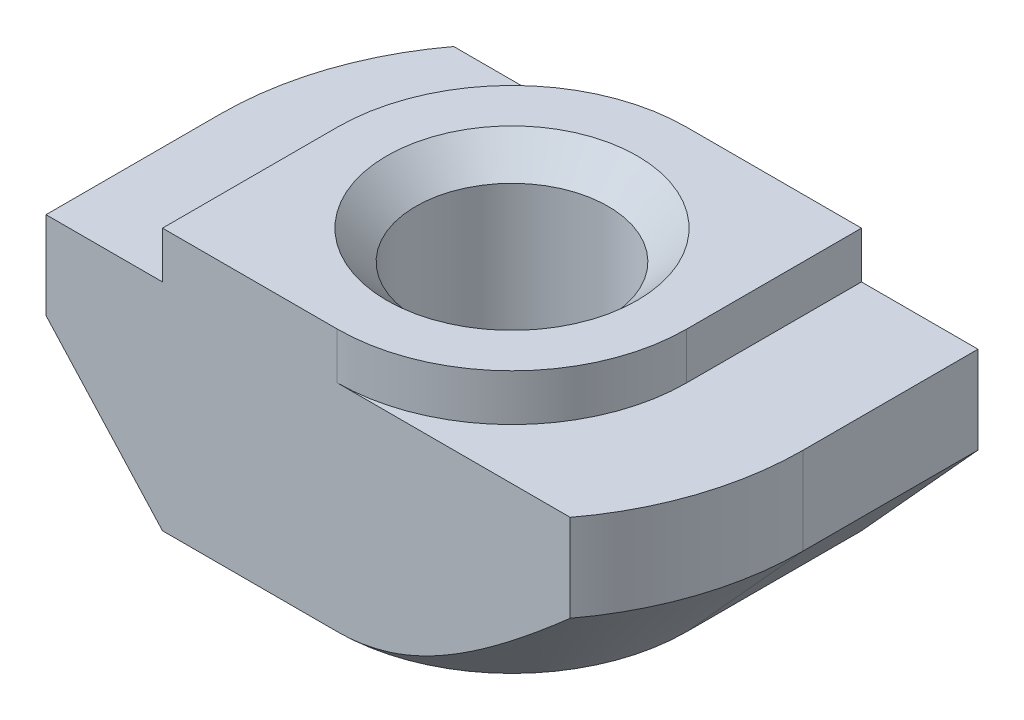
SolidWorks part; units mm, degrees
material "Сталь 20  ГОСТ 1050-2013"
ref_plane "Спереди" through (0, 0, 0) normal (0, 0, 1) x (1, 0, 0)
ref_plane "Сверху" through (0, 0, 0) normal (0, 1, 0) x (1, 0, 0)
ref_plane "Справа" through (0, 0, 0) normal (1, 0, 0) x (0, 0, -1)
sketch "Эскиз1" plane through (0, 0, 0) normal (0, 0, 1) x (1, 0, 0)
  line L0 (3, 0) -> (-3, 0)
  line L1 (-3, 0) -> (-3, -0.8)
  line L2 (-3, -0.8) -> (-5, -0.8)
  line L3 (-5, -0.8) -> (-5, -4.5)
  line L4 (-5, -4.5) -> (5, -4.5)
  line L5 (0, -4.5) -> (0, 0) construction
  line L6 (5, -0.8) -> (5, -4.5)
  line L7 (3, -0.8) -> (5, -0.8)
  line L8 (3, 0) -> (3, -0.8)
  dimension "D1" = 6
  dimension "D2" = 10
  dimension "D3" = 4.5
  dimension "D4" = 0.8
extrude "Бобышка-Вытянуть1" add sketch "Эскиз1" along normal mid plane 6
hole_wizard "Отверстие обработанное метчиком M41" positions "Эскиз2" profile "Эскиз3" tap size "M4" standard "ISO" end condition up to next
sketch "Эскиз2" plane through (0, 0, 0) normal (0, 1, 0) x (1, 0, 0)
  point P0 (0, 0)
sketch "Эскиз3" plane through (0, 0, 0) normal (1, 0, 0) x (0, 0, 1)
  line L0 (0, 0) -> (0, 4.5)
  line L1 (0, 4.5) -> (2.15, 4.5)
  line L2 (1.65, 4) -> (1.65, 0.5)
  line L3 (1.65, 0.5) -> (2.15, 0)
  line L5 (2.15, 0) -> (0, 0)
  line L6 (-1.65, 0.5) -> (-2.15, 0) construction
  line L7 (2.15, 4.5) -> (1.65, 4)
  line L8 (-2.15, 4.5) -> (-1.65, 4) construction
  line L11 (0, -6.35) -> (0, 107.95) construction
  dimension "Диаметр проходного сверла" = 3.3
  dimension "Глубина проходного сверла" = 4.5
  dimension "Диаметр передней зенковки" = 4.3
  dimension "Угол передней зенковки" = 90
  dimension "Диаметр задней зенковки" = 4.3
  dimension "Угол задней зенковки" = 90
cosmetic thread "Отверстие резьбы1" parameters "D2"=4
sketch "Эскиз4" plane through (0, 0, 0) normal (0, 1, 0) x (1, 0, 0)
  line L0 (-3, 3) -> (-3, 0)
  line L1 (-3, -3) -> (-3, 3) construction
  line L2 (3, 3) -> (-3, 3) construction
  line L3 (0, 3) -> (-3, 3)
  line L4 (0, -3) -> (3, -3)
  line L5 (3, -3) -> (-3, -3) construction
  line L6 (3, -3) -> (3, 0)
  line L7 (3, -3) -> (3, 3) construction
  arc A0 (-3, 0) -> (0, 3) centre (0, 0) cw
  arc A1 (3, 0) -> (0, -3) centre (0, 0) cw
extrude "Вырез-Вытянуть1" cut sketch "Эскиз4" against normal up to surface (0.8 mm away) up to face at (-4, -0.8, 0)
sketch "Эскиз5" plane through (0, -0.8, 0) normal (0, 1, 0) x (1, 0, 0)
  line L0 (-5, 0) -> (-5, 3)
  line L1 (-5, -3) -> (-5, 3) construction
  line L2 (-5, 3) -> (-4, 3)
  line L3 (0, 3) -> (-5, 3) construction
  line L4 (5, 0) -> (5, -3)
  line L5 (5, -3) -> (5, 3) construction
  line L6 (5, -3) -> (4, -3)
  line L7 (5, -3) -> (0, -3) construction
  arc A0 (-4, 3) -> (-5, 0) centre (0, 0) ccw
  arc A2 (5, 0) -> (4, -3) centre (0, 0) cw
  point P19 (0, 0)
extrude "Вырез-Вытянуть2" cut sketch "Эскиз5" against normal through all
sketch "Эскиз6" plane through (0, 0, 3) normal (0, 0, 1) x (1, 0, 0)
  line L0 (-5, -2.3) -> (-5, -4.5)
  line L1 (-5, -0.8) -> (-5, -4.5) construction
  line L2 (-5, -4.5) -> (-3, -4.5)
  line L3 (-5, -4.5) -> (4, -4.5) construction
  line L4 (-3, -4.5) -> (-5, -2.3)
  line L5 (-3, -0.8) -> (-5, -0.8) construction
  line L6 (-3, 0) -> (-3, -0.8) construction
  point P10 (0, 0)
  dimension "D1" = 1.5
sketch "Эскиз7" plane through (0, -4.5, 0) normal (0, -1, 0) x (1, 0, 0)
  line L0 (0, 5) -> (-5, 5)
  line L1 (-5, 5) -> (-5, 0)
  line L2 (0, -5) -> (5, -5)
  line L3 (5, -5) -> (5, 0)
  arc A0 (-5, 0) -> (0, -5) centre (0, 0) ccw
  arc A1 (5, 0) -> (0, 5) centre (0, 0) ccw
sweep "Вырез-По траектории1" cut profiles "Эскиз6" path "Эскиз7"
